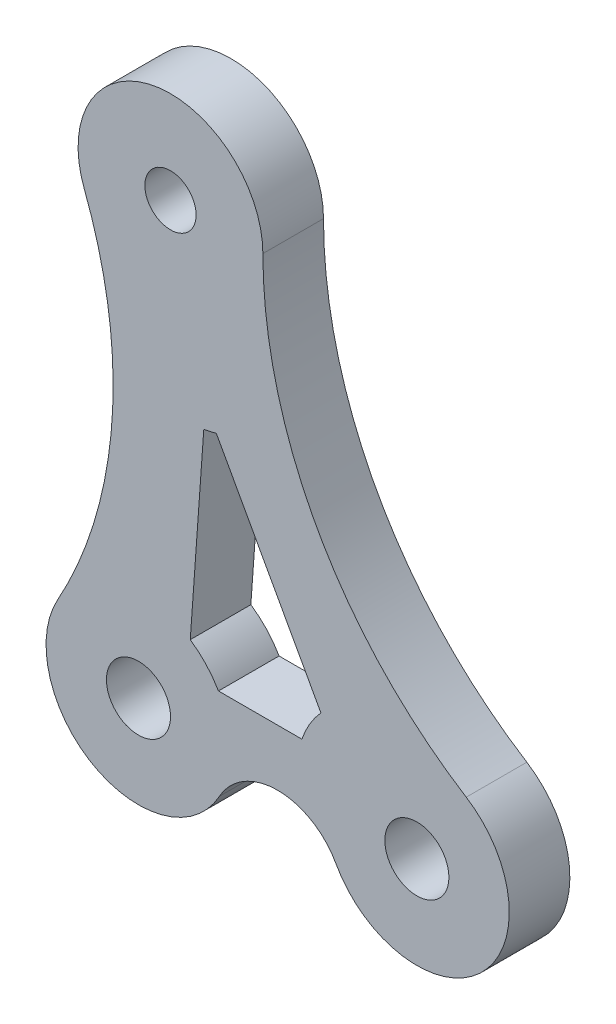
SolidWorks part; units mm, degrees
ref_plane "Alzado" through (0, 0, 0) normal (0, 0, 1) x (1, 0, 0)
ref_plane "Planta" through (0, 0, 0) normal (0, 1, 0) x (1, 0, 0)
ref_plane "Vista lateral" through (0, 0, 0) normal (1, 0, 0) x (0, 0, -1)
sketch "Croquis1" plane through (0, 0, 0) normal (0, 0, 1) x (1, 0, 0)
  line L0 (0, 23.0505) -> (0, 0) construction
  line L1 (0, 0) -> (12.7, 0) construction
  line L2 (0, 23.0505) -> (-1.651, 0) construction
  line L3 (4.7503, 22.7103) -> (3.0993, -0.3402)
  line L4 (-4.7503, 23.3907) -> (-6.4013, 0.3402)
  line L5 (-1.651, 0) -> (12.7, 0) construction
  line L6 (-1.651, 4.7625) -> (12.7, 4.7625)
  line L7 (-1.651, -4.7625) -> (12.7, -4.7625)
  line L8 (0, 23.0505) -> (12.7, 0) construction
  line L9 (4.1713, 25.3487) -> (16.8713, 2.2982)
  line L10 (-4.1713, 20.7523) -> (8.5287, -2.2982)
  circle A0 centre (0, 23.0505) radius 1.3208
  circle A1 centre (0, 0) radius 1.651
  circle A2 centre (12.7, 0) radius 1.651
  circle A3 centre (-1.651, 0) radius 1.651
  arc A4 (4.7503, 22.7103) -> (-4.7503, 23.3907) centre (0, 23.0505) ccw
  arc A5 (-6.4013, 0.3402) -> (3.0993, -0.3402) centre (-1.651, 0) ccw
  arc A6 (-1.651, 4.7625) -> (-1.651, -4.7625) centre (-1.651, 0) ccw
  arc A7 (12.7, -4.7625) -> (12.7, 4.7625) centre (12.7, 0) ccw
  arc A8 (4.1713, 25.3487) -> (-4.1713, 20.7523) centre (0, 23.0505) ccw
  arc A9 (8.5287, -2.2982) -> (16.8713, 2.2982) centre (12.7, 0) ccw
  arc A10 (8.5287, -2.2982) -> (2.5203, -2.2982) centre (5.5245, -3.9534) ccw
  arc A11 (4.7625, 23.0505) -> (15.2444, 4.0258) centre (27.2683, 23.0505) ccw
  arc A12 (-4.4469, 21.3458) -> (-5.8096, 2.3211) centre (-25.4616, 13.2898) cw
  point P9 (-0.8255, 11.5252)
  point P14 (5.5245, 0)
  point P22 (6.35, 11.5252)
  dimension "D1" = 3.302
  dimension "D2" = 23.0505
  dimension "D4" = 9.525
  dimension "D6" = 2.6416
  dimension "D3" = 12.7
  dimension "D5" = 9.525
extrude "Saliente-Extruir1" add sketch "Croquis1" along normal blind 3.1242 contours A8 L4 A6 L6 L3 L10 | A7 L9 A4 L3 L10 L6 | L10 A9 A7 L6 A2 | A9 L10 L6 L3 A5 L7 | L6 A6 A5 L3 A3 A1 | A4 A8 L10 L3 A0 | A3 A1
sketch "Croquis2" plane through (0, 0, 3.1242) normal (0, 0, 1) x (1, 0, 0)
  line L0 (0, 23.0505) -> (-1.651, 0) construction
  line L1 (-1.651, 0) -> (12.7, 0) construction
  line L2 (12.7, 0) -> (0, 23.0505) construction
  line L3 (8.6693, 2.3812) -> (1.7999, 14.8491)
  line L4 (1.7999, 14.8491) -> (0.9069, 2.3812)
  line L5 (0.9069, 2.3812) -> (8.6693, 2.3812)
  line L6 (11.2785, 0.8398) -> (12.7, 0) construction
  line L7 (1.0209, 18.3987) -> (0, 23.0505) construction
  circle A0 centre (0, 23.0505) radius 4.7625
  circle A1 centre (-1.651, 0) radius 4.7625
  circle A2 centre (12.7, 0) radius 4.7625
  arc A3 (4.7625, 23.0505) -> (-4.4469, 21.3458) centre (0, 23.0505) ccw construction
  arc A4 (2.362, 13.8289) -> (1.7167, 13.6873) centre (1.0209, 18.3987) cw
  arc A5 (7.7539, 4.0426) -> (6.7724, 2.3813) centre (11.2785, 0.8398) ccw
  circle A6 centre (12.7, 0) radius 1.651 construction
  arc A7 (8.5287, -2.2982) -> (2.5203, -2.2982) centre (5.5245, -3.9534) ccw construction
  point P23 (5.5245, -0.5234)
  line M10 (3.5998, 6.6477) -> (4.6385, 4.7625)
  line M11 (4.6385, 4.7625) -> (3.4648, 4.7625)
  line M12 (3.4648, 4.7625) -> (3.5998, 6.6477)
  dimension "D1" = 2.3812
  dimension "D2" = 32.95
  dimension "61." = 30.575
  dimension "D3" = 61.147
  dimension "D4" = 16.475
  dimension "D5" = 2.9047
extrude "Cortar-Extruir1" cut sketch "Croquis2" against normal blind 3.1242 contours A1 L5 L3 L4 M12 M10 M11
